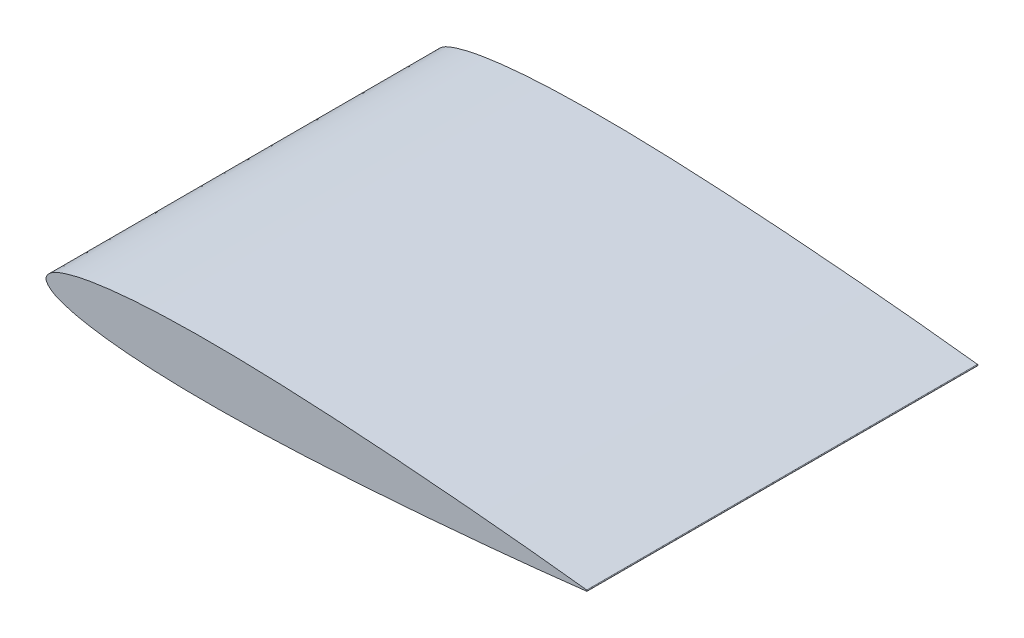
SolidWorks part; units mm, degrees
ref_plane "Front Plane" through (0, 0, 0) normal (0, 0, 1) x (1, 0, 0)
ref_plane "Top Plane" through (0, 0, 0) normal (0, 1, 0) x (1, 0, 0)
ref_plane "Right Plane" through (0, 0, 0) normal (1, 0, 0) x (0, 0, -1)
curve "Curve1"
  spline degree 3 poles (84.4, 0.0886, 0) (82.9935, 0.25, 0) (80.1816, 0.5727, 0) (74.5562, 1.1724, 0) (67.5244, 1.8616, 0) (59.0839, 2.592, 0) (50.644, 3.2291, 0) (42.204, 3.7485, 0) (33.7634, 4.1181, 0) (26.727, 4.2473, 0) (21.0989, 4.1962, 0) (16.8769, 4.0573, 0) (12.6519, 3.7894, 0) (9.1337, 3.4161, 0) (6.3183, 2.9686, 0) (4.2023, 2.5316, 0) (2.4032, 1.9764, 0) (0.9111, 1.3483, 0) (-0.5395, 0, 0) (0.9111, -1.3483, 0) (2.4032, -1.9764, 0) (4.2023, -2.5316, 0) (6.3183, -2.9686, 0) (9.1337, -3.4161, 0) (12.6519, -3.7894, 0) (16.8769, -4.0573, 0) (21.0989, -4.1962, 0) (26.727, -4.2473, 0) (33.7634, -4.1181, 0) (42.204, -3.7485, 0) (50.644, -3.2291, 0) (59.0839, -2.592, 0) (67.5244, -1.8616, 0) (74.5562, -1.1724, 0) (80.1816, -0.5727, 0) (82.9935, -0.25, 0) (84.4, -0.0886, 0) knots 0 0 0 0 0.024824 0.04963 0.099197 0.148713 0.198182 0.247604 0.29698 0.346318 0.370984 0.395664 0.420382 0.445198 0.457689 0.470304 0.483229 0.490069 0.5 0.509931 0.516771 0.529696 0.542311 0.554802 0.579618 0.604336 0.629016 0.653682 0.70302 0.752396 0.801818 0.851287 0.900803 0.95037 0.975176 1 1 1 1
sketch "Sketch1" plane through (0, 0, 0) normal (0, 0, 1) x (1, 0, 0)
  arc A0 (84.4, 0.0886) -> (84.4, -0.0886) centre (84.3898, 0) cw
  spline S0 degree 3 poles (752.2237, 2912.9652) (305.0924, -62.4173) (193.3756, -11.4933) (74.5562, 1.1724) (67.5244, 1.8616) (59.0839, 2.592) (50.644, 3.2291) (42.204, 3.7485) (33.7634, 4.1181) (26.727, 4.2473) (21.0989, 4.1962) (16.8769, 4.0573) (12.6519, 3.7894) (9.1337, 3.4161) (6.3183, 2.9686) (4.2023, 2.5316) (2.4032, 1.9764) (0.9111, 1.3483) (-0.5395, 0) (0.9111, -1.3483) (2.4032, -1.9764) (4.2023, -2.5316) (6.3183, -2.9686) (9.1337, -3.4161) (12.6519, -3.7894) (16.8769, -4.0573) (21.0989, -4.1962) (26.727, -4.2473) (33.7634, -4.1181) (42.204, -3.7485) (50.644, -3.2291) (59.0839, -2.592) (67.5244, -1.8616) (74.5562, -1.1724) (193.3754, 11.4933) (305.092, 62.4171) (752.2211, -2912.9476) knots -1.996049 -1.996049 -1.996049 -1.996049 0.024824 0.04963 0.099197 0.148713 0.198182 0.247604 0.29698 0.346318 0.370984 0.395664 0.420382 0.445198 0.457689 0.470304 0.483229 0.490069 0.5 0.509931 0.516771 0.529696 0.542311 0.554802 0.579618 0.604336 0.629016 0.653682 0.70302 0.752396 0.801818 0.851287 0.900803 0.95037 0.975176 2.996045 2.996045 2.996045 2.996045 only from (84.4, 0.0886) to (84.4, -0.0886) construction
  spline S1 degree 3 poles (84.4, 0.0886) (82.9935, 0.25) (80.1816, 0.5727) (74.5562, 1.1724) (67.5244, 1.8616) (59.0839, 2.592) (50.644, 3.2291) (42.204, 3.7485) (33.7634, 4.1181) (26.727, 4.2473) (21.0989, 4.1962) (16.8769, 4.0573) (12.6519, 3.7894) (9.1337, 3.4161) (6.3183, 2.9686) (4.2023, 2.5316) (2.4032, 1.9764) (0.9111, 1.3483) (-0.5395, 0) (0.9111, -1.3483) (2.4032, -1.9764) (4.2023, -2.5316) (6.3183, -2.9686) (9.1337, -3.4161) (12.6519, -3.7894) (16.8769, -4.0573) (21.0989, -4.1962) (26.727, -4.2473) (33.7634, -4.1181) (42.204, -3.7485) (50.644, -3.2291) (59.0839, -2.592) (67.5244, -1.8616) (74.5562, -1.1724) (80.1816, -0.5727) (82.9935, -0.25) (84.4, -0.0886) knots 0 0 0 0 0.024824 0.04963 0.099197 0.148713 0.198182 0.247604 0.29698 0.346318 0.370984 0.395664 0.420382 0.445198 0.457689 0.470304 0.483229 0.490069 0.5 0.509931 0.516771 0.529696 0.542311 0.554802 0.579618 0.604336 0.629016 0.653682 0.70302 0.752396 0.801818 0.851287 0.900803 0.95037 0.975176 1 1 1 1
extrude "Boss-Extrude1" add sketch "Sketch1" along normal blind 61
